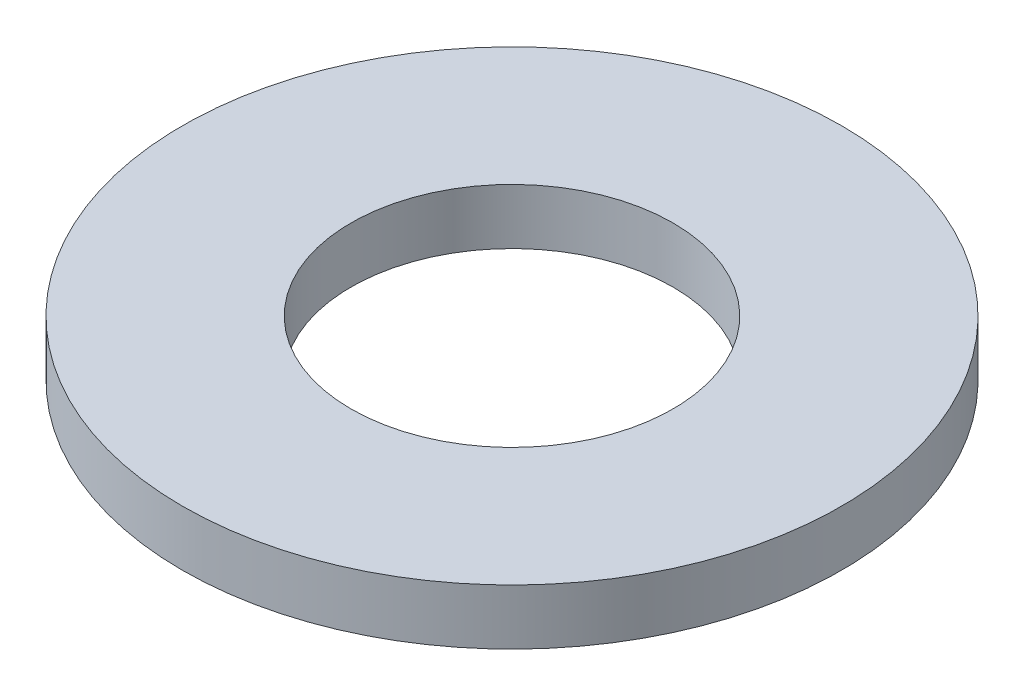
SolidWorks part; units mm, degrees
ref_plane "Front Plane" through (0, 0, 0) normal (0, 0, 1) x (1, 0, 0)
ref_plane "Top Plane" through (0, 0, 0) normal (0, 1, 0) x (1, 0, 0)
ref_plane "Right Plane" through (0, 0, 0) normal (1, 0, 0) x (0, 0, -1)
sketch "Sketch2" plane through (0, 0, 0) normal (0, 1, 0) x (1, 0, 0)
  circle A0 centre (0, 0) radius 4.45
  circle A1 centre (0, 0) radius 2.175
  dimension "D1" = 8.9
  dimension "D2" = 4.35
extrude "Boss-Extrude1" add sketch "Sketch2" along normal blind 0.75
